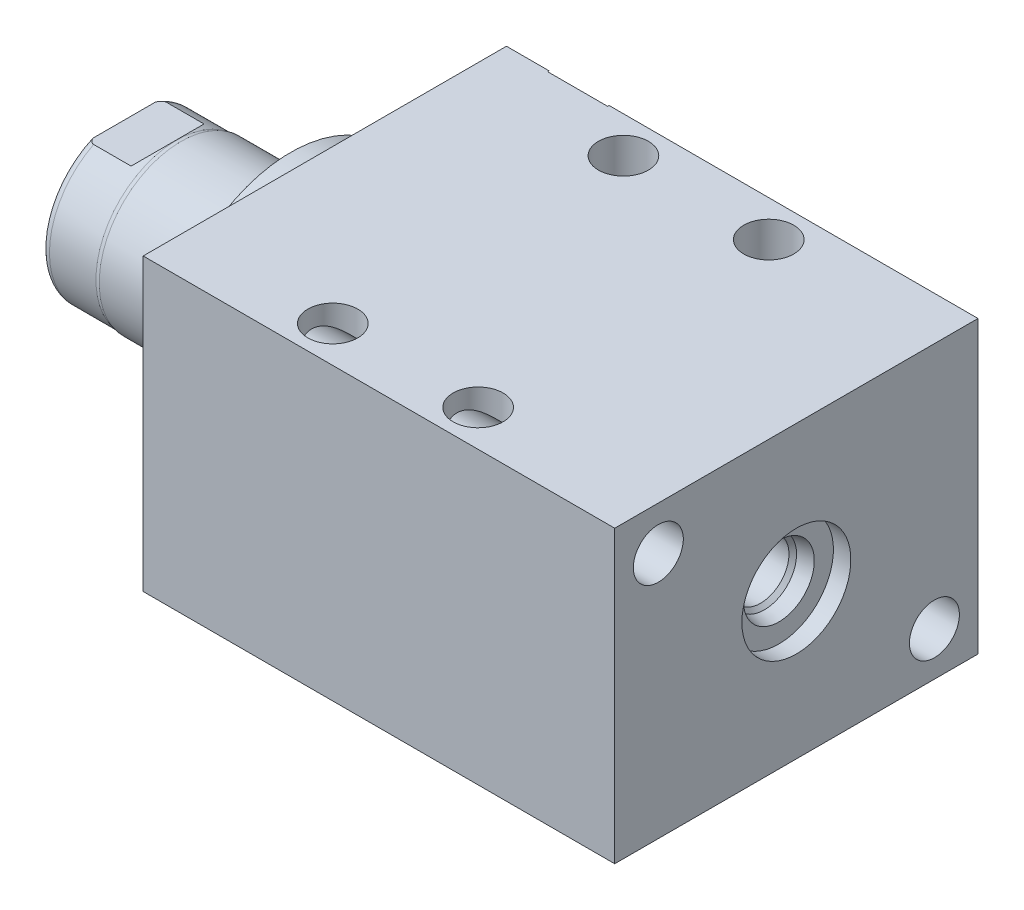
SolidWorks part; units mm, degrees
material "Alloy Steel"
ref_plane "Front Plane" through (0, 0, 0) normal (0, 0, 1) x (1, 0, 0)
ref_plane "Top Plane" through (0, 0, 0) normal (0, 1, 0) x (1, 0, 0)
ref_plane "Right Plane" through (0, 0, 0) normal (1, 0, 0) x (0, 0, -1)
ref_plane "Plane1" through (0, 0, 0) normal (1, 0, 0) x (0, 0, -1)
sketch "Sketch1" plane through (0, 0, 0) normal (1, 0, 0) x (0, 0, -1)
  line L0 (-31.75, 25.4) -> (31.75, 25.4)
  line L1 (31.75, 25.4) -> (31.75, -25.4)
  line L2 (31.75, -25.4) -> (-31.75, -25.4)
  line L3 (-31.75, -25.4) -> (-31.75, 25.4)
  line L4 (0, -24.4475) -> (0, 24.4475) construction
  dimension "D1" = 50.8
  dimension "D2" = 25.4
  dimension "D3" = 63.5
extrude "Extrude1" add sketch "Sketch1" along normal blind 82.423
ref_plane "Plane12" through (0, 17.4498, 0) normal (0, 1, 0) x (-1, 0, 0)
sketch "S2D0002" plane through (0, 17.4498, 0) normal (0, 1, 0) x (-1, 0, 0)
  line L0 (-18.8849, -31.496) -> (-22.225, -31.496)
  line L1 (-18.8849, -31.496) -> (-18.3423, -28.9433)
  line L2 (-18.3423, -28.9433) -> (-17.6784, -28.2794)
  line L3 (-17.6784, -28.2794) -> (-17.6784, -17.526)
  line L4 (-17.6784, -17.526) -> (-12.7, -17.526)
  line L5 (-12.7, -17.526) -> (-12.7, -31.75)
  line L6 (-12.7, -19.1384) -> (-12.7, 0.6985) construction
  line L7 (0, -31.75) -> (0, 31.75) construction
  line L8 (-22.225, -31.75) -> (-22.225, -31.496)
  line L9 (-82.423, -31.75) -> (0, -31.75) construction
  line L10 (-22.225, -31.75) -> (-12.7, -31.75)
  dimension "D1" = 14.224
  dimension "D2" = 12.7
  dimension "D3" = 9.9568
  dimension "D4" = 45
  dimension "D5" = 12.3698
  dimension "D6" = 12
  dimension "D7" = 2.5527
  dimension "D8" = 0.254
  dimension "D9" = 19.05
revolve "Cut-Revolve1" cut sketch "S2D0002" angle 360 about L6
ref_plane "Plane3" through (41.148, 0, -25.146) normal (0, 1, 0) x (1, 0, 0)
sketch "Sketch3" plane through (41.148, 0, -25.146) normal (0, 1, 0) x (1, 0, 0)
  line L0 (31.5849, 6.35) -> (34.925, 6.35)
  line L1 (31.5849, 6.35) -> (31.0423, 3.7973)
  line L2 (31.0423, 3.7973) -> (30.3784, 3.1334)
  line L3 (30.3784, 3.1334) -> (30.3784, -7.62)
  line L4 (30.3784, -7.62) -> (25.4, -7.62)
  line L5 (25.4, -7.62) -> (25.4, 6.604)
  line L6 (25.4, -21.9564) -> (25.4, 0.6985) construction
  line L7 (-41.148, 6.604) -> (-41.148, -56.896) construction
  line L8 (34.925, 6.604) -> (34.925, 6.35)
  line L9 (41.275, 6.604) -> (-23.2021, 6.604) construction
  line L10 (34.925, 6.604) -> (25.4, 6.604)
  dimension "D1" = 14.224
  dimension "D2" = 66.548
  dimension "D3" = 9.9568
  dimension "D4" = 45
  dimension "D5" = 12
  dimension "D6" = 12.3698
  dimension "D7" = 2.5527
  dimension "D8" = 0.254
  dimension "D9" = 19.05
revolve "Cut-Revolve2" cut sketch "Sketch3" angle 360 about L6
ref_plane "Plane4" through (53.975, 0, 0) normal (0, 0, 1) x (0, -1, 0)
sketch "Sketch4" plane through (53.975, 0, 0) normal (0, 0, 1) x (0, -1, 0)
  line L0 (6.1849, 25.4) -> (9.525, 25.4)
  line L1 (6.1849, 25.4) -> (5.6423, 22.8473)
  line L2 (5.6423, 22.8473) -> (4.9784, 22.1834)
  line L3 (4.9784, 22.1834) -> (4.9784, 14.0462)
  line L4 (4.9784, 14.0462) -> (0, 14.0462)
  line L5 (0, 14.0462) -> (0, 28.448)
  line L6 (0, -15.0954) -> (0, 0.5677) construction
  line L7 (0, 28.448) -> (9.525, 28.448)
  line L9 (-25.4, 28.448) -> (25.4, 28.448) construction
  line L10 (9.525, 28.448) -> (9.525, 25.4)
  dimension "D1" = 11.3538
  dimension "D2" = 9.9568
  dimension "D3" = 3.048
  dimension "D4" = 19.05
  dimension "D5" = 2.5527
  dimension "D6" = 12
  dimension "D7" = 45
  dimension "D8" = 12.3698
revolve "Cut-Revolve3" cut sketch "Sketch4" angle 360 about L6
sketch "Sketch5" plane through (0, 0, 0) normal (-1, 0, 0) x (0, 0, 1)
  circle A0 centre (0, 0) radius 22.225
  dimension "D1" = 44.45
extrude "Extrude2" add sketch "Sketch5" along normal blind 5.969
ref_plane "Plane5" through (0, 0, 0) normal (0, -1, 0) x (0, 0, 1)
sketch "Sketch6" plane through (0, 0, 0) normal (0, -1, 0) x (0, 0, 1)
  line L0 (0, 5.969) -> (-14.2875, 5.969)
  line L1 (-14.2875, 5.969) -> (-14.2875, 35.052)
  line L2 (-14.2875, 35.052) -> (0, 35.052)
  line L3 (0, 35.052) -> (0, 5.969)
  line L4 (0, -5.7546) -> (0, 21.1709) construction
  line L5 (22.225, 5.969) -> (-22.225, 5.969) construction
  line L6 (31.75, -82.423) -> (-31.75, -82.423) construction
  dimension "D1" = 117.475
  dimension "D2" = 28.575
revolve "Revolve1" add sketch "Sketch6" angle 360 about L4
ref_plane "Plane6" through (-18.5113, 3.2639, 0) normal (0, 0, 1) x (0, 1, 0)
sketch "S2D0001" plane through (-18.5113, 3.2639, 0) normal (0, 0, 1) x (0, 1, 0)
  line L0 (2.286, 14.473) -> (2.286, -1.9505)
  line L1 (2.286, -1.9505) -> (-3.2639, -1.9505)
  line L2 (3.4798, 16.5407) -> (-3.2639, 16.5407)
  line L3 (-3.2639, 16.5407) -> (-3.2639, -1.9505)
  line L4 (2.286, 14.473) -> (3.4798, 16.5407)
  line L5 (-3.2639, -18.5113) -> (-3.2639, 2.765) construction
  line L6 (11.0236, 16.5407) -> (-17.5514, 16.5407) construction
  dimension "D1" = 30
  dimension "D2" = 13.4874
  dimension "D3" = 11.0998
  dimension "D4" = 18.4912
revolve "Cut-Revolve4" cut sketch "S2D0001" angle 360 about L5
ref_plane "Plane7" through (0, 0, 0) normal (0, 1, 0) x (0, 0, -1)
sketch "Sketch8" plane through (0, 0, 0) normal (0, 1, 0) x (0, 0, -1)
  line L0 (-14.2875, 25.146) -> (-14.097, 25.908)
  line L1 (-14.097, 25.908) -> (-14.097, 34.036)
  line L2 (0, 12.6594) -> (0, 20.8178) construction
  line L3 (-14.2875, 25.146) -> (-14.2875, 35.052)
  line L4 (-13.7089, 35.052) -> (-14.2875, 35.052)
  line L5 (14.2875, 35.052) -> (-14.2875, 35.052) construction
  line L6 (-14.2875, 35.052) -> (-14.2875, 5.969) construction
  arc A0 (-13.7089, 35.052) -> (-14.097, 34.036) centre (-12.573, 34.036) ccw
  dimension "D2" = 1.524
  dimension "D1" = 28.194
  dimension "D3" = 1.016
  dimension "D4" = 0.762
  dimension "D5" = 9.144
revolve "Cut-Revolve5" cut sketch "Sketch8" angle 360 about L2
ref_plane "Plane11" through (0, 0, 0) normal (0, 0, -1) x (0, -1, 0)
sketch "Sketch12" plane through (0, 0, 0) normal (0, 0, -1) x (0, -1, 0)
  line L0 (12.573, 35.052) -> (12.573, 27.4828)
  line L1 (12.573, 27.4828) -> (14.097, 25.9588)
  line L2 (-12.573, 35.052) -> (-12.573, 27.4828)
  line L3 (-12.573, 27.4828) -> (-14.097, 25.9588)
  line L4 (12.573, 35.052) -> (14.097, 35.052)
  line L5 (0, 13.7262) -> (0, 20.767) construction
  line L6 (-14.097, 25.9588) -> (-14.097, 35.052)
  line L7 (13.7089, 35.052) -> (-13.7089, 35.052) construction
  line L8 (14.097, 25.908) -> (14.097, 34.036) construction
  line L9 (14.097, 25.9588) -> (14.097, 35.052)
  line L10 (-12.573, 35.052) -> (-14.097, 35.052)
  dimension "D1" = 25.146
  dimension "D2" = 7.5692
  dimension "D3" = 45
extrude "Cut-Extrude4" cut sketch "Sketch12" against normal mid plane 60.96
hole_wizard "Hole1" positions "Sketch15" profile "Sketch14" legacy end condition up to next
sketch "Sketch15" plane through (0, 0, 0) normal (-1, 0, 0) x (0, 0, 1)
  line L0 (0, 0) -> (-29.9914, 0) construction
  line L1 (0, 0) -> (0, 25.7648) construction
  point P0 (-24.13, -17.78)
  point P11 (24.13, 17.78)
  dimension "D1" = 17.78
  dimension "D2" = 24.13
  dimension "D3" = 35.56
  dimension "D4" = 48.26
sketch "Sketch14" plane through (0, -17.78, -24.13) normal (0, 1, 0) x (0, 0, 1)
  line L0 (0, 0) -> (0, 82.423)
  line L1 (0, 82.423) -> (4.3688, 82.423)
  line L2 (4.3688, 82.423) -> (4.3688, 0)
  line L3 (4.3688, 0) -> (0, 0)
  line L4 (0, 110) -> (0, -10) construction
  dimension "Diameter" = 8.7376
  dimension "Depth" = 82.423
hole_wizard "Hole2" positions "Sketch17" profile "Sketch16" legacy
sketch "Sketch17" plane through (0, 25.4, 0) normal (0, 1, 0) x (-1, 0, 0)
  line L0 (0, 0) -> (-59.3363, 0) construction
  line L1 (0, -31.75) -> (0, 31.75) construction
  point P0 (-26.797, -25.4)
  point P9 (-26.797, 25.4)
  dimension "D1" = 50.8
  dimension "D2" = 26.797
sketch "Sketch16" plane through (26.797, 25.4, -25.4) normal (1, 0, 0) x (0, 0, 1)
  line L0 (0, 0) -> (0, 50.8)
  line L1 (0, 50.8) -> (4.3688, 50.8)
  line L2 (4.3688, 50.8) -> (4.3688, 0)
  line L3 (4.3688, 0) -> (0, 0)
  line L4 (0, 110) -> (0, -10) construction
  dimension "Diameter" = 8.7376
  dimension "Depth" = 50.8
pattern_linear "LPattern1" count 2 spacing 25.4 along (1, 0, 0) of "Hole2"
